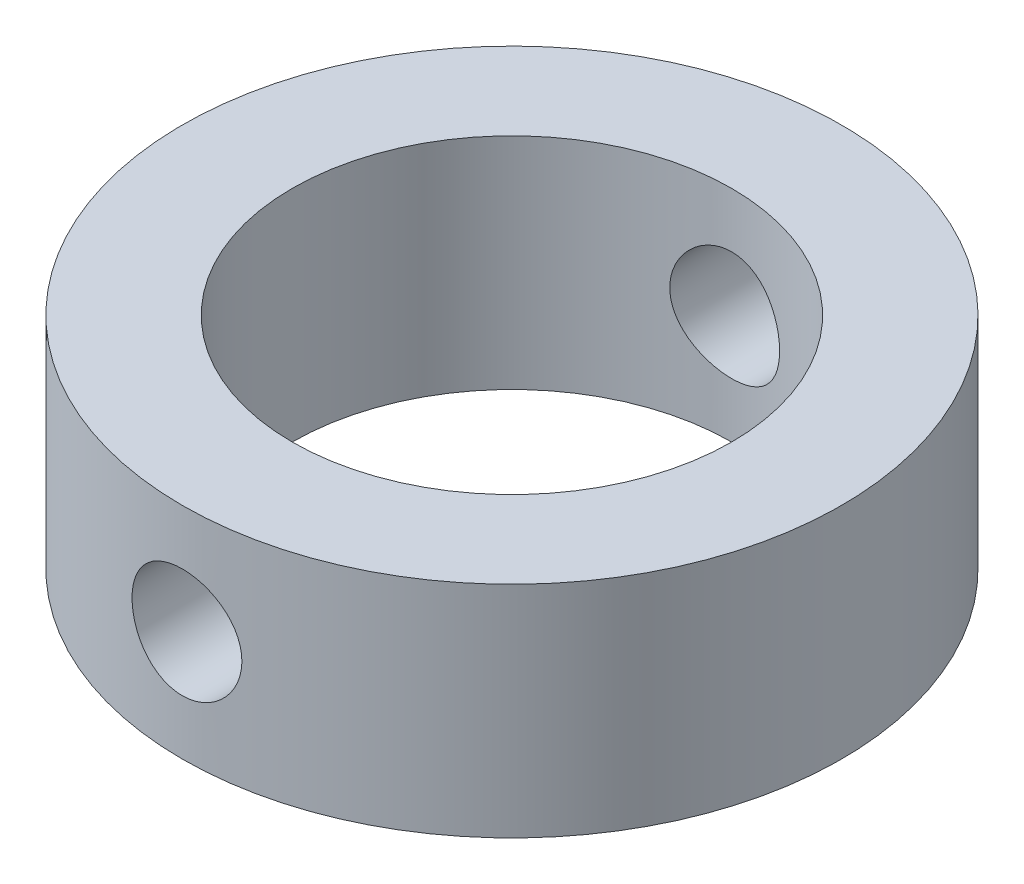
SolidWorks part; units mm, degrees
ref_plane "Front Plane" through (0, 0, 0) normal (0, 0, 1) x (1, 0, 0)
ref_plane "Top Plane" through (0, 0, 0) normal (0, 1, 0) x (1, 0, 0)
ref_plane "Right Plane" through (0, 0, 0) normal (1, 0, 0) x (0, 0, -1)
sketch "Sketch1" plane through (0, 0, 0) normal (0, 1, 0) x (1, 0, 0)
  circle A0 centre (0, 0) radius 12
  circle A1 centre (0, 0) radius 8
  dimension "D1" = 24
  dimension "D2" = 16
extrude "Boss-Extrude1" add sketch "Sketch1" along normal blind 8
sketch "Sketch2" plane through (0, 0, 0) normal (0, 0, 1) x (1, 0, 0)
  line L0 (12, 0) -> (12, 8) construction
  circle A0 centre (0, 4) radius 2
  dimension "D1" = 4
  dimension "D2" = 4
  dimension "D3" = 12
extrude "Cut-Extrude1" cut sketch "Sketch2" against normal blind 17 and the other way blind 18
